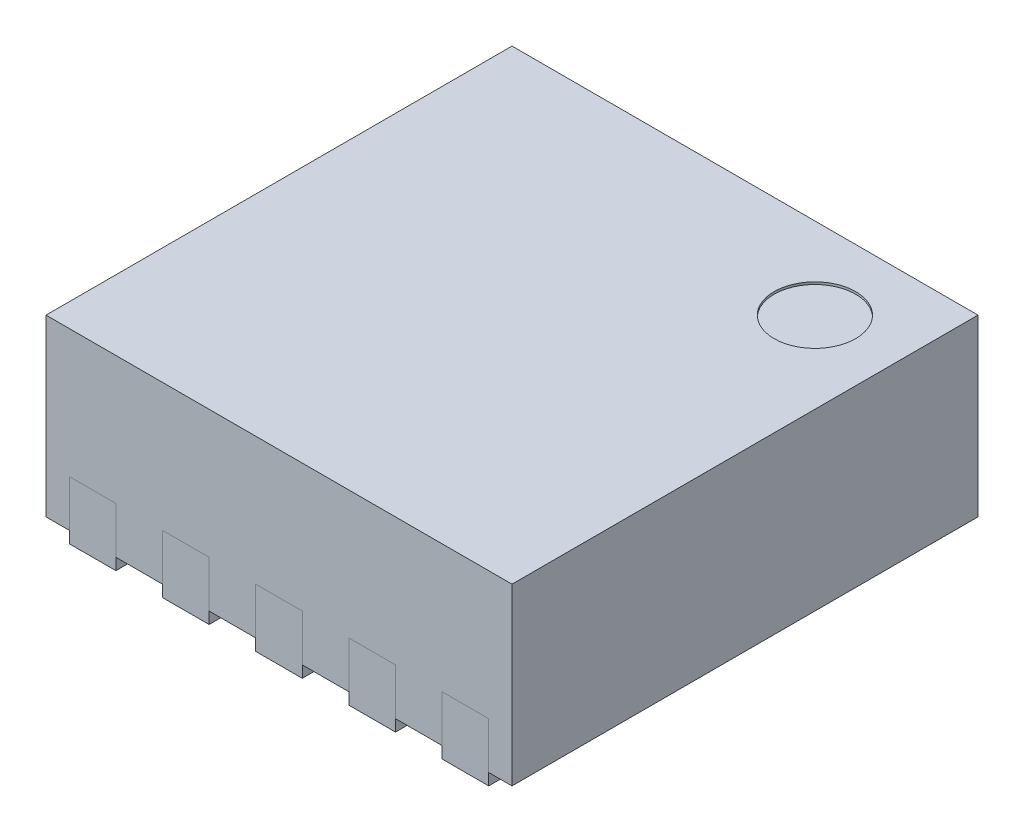
SolidWorks part; units mm, degrees
ref_plane "Front Plane" through (0, 0, 0) normal (0, 0, 1) x (1, 0, 0)
ref_plane "Top Plane" through (0, 0, 0) normal (0, 1, 0) x (1, 0, 0)
ref_plane "Right Plane" through (0, 0, 0) normal (1, 0, 0) x (0, 0, -1)
sketch "Sketch1" plane through (0, 0, 0) normal (0, 1, 0) x (1, 0, 0)
  line L1 (1, 1) -> (-1, 1)
  line L2 (1, 1) -> (1, -1)
  line L3 (1, -1) -> (-1, -1)
  line L4 (-1, 1) -> (-1, -1)
  line L5 (1, 1) -> (-1, -1) construction
  line L6 (1, -1) -> (-1, 1) construction
  point P0 (0, 0)
  dimension "D1" = 2
extrude "Boss-Extrude1" add sketch "Sketch1" along normal blind 0.75
sketch "Sketch2" plane through (0, 0, 0) normal (0, -1, 0) x (1, 0, 0)
  line L0 (0, 1) -> (0, 0) construction
  line L1 (-1, 1) -> (1, 1) construction
  line L2 (0.3, 0.7) -> (0.5, 0.7)
  line L3 (-0.1, 0.7) -> (0.1, 0.7)
  line L4 (-0.1, 0.7) -> (-0.1, 1)
  line L5 (-0.1, 1) -> (0.1, 1)
  line L6 (0.1, 0.7) -> (0.1, 1)
  line L7 (-0.1, 0.7) -> (0.1, 1) construction
  line L8 (-0.1, 1) -> (0.1, 0.7) construction
  line L9 (0.3, 0.7) -> (0.3, 1)
  line L10 (0.3, 1) -> (0.5, 1)
  line L11 (0.5, 0.7) -> (0.5, 1)
  line L12 (0.7, 0.7) -> (0.9, 0.7)
  line L13 (0.7, 0.7) -> (0.7, 1)
  line L14 (0.7, 1) -> (0.9, 1)
  line L15 (0.9, 0.7) -> (0.9, 1)
  line L16 (-0.1, 0.7) -> (0.1, 0.7)
  line L17 (-0.1, 0.7) -> (-0.1, 1)
  line L18 (-0.1, 1) -> (0.1, 1)
  line L19 (0.1, 0.7) -> (0.1, 1)
  line L20 (0.3, 0.7) -> (0.5, 0.7)
  line L21 (0.3, 0.7) -> (0.3, 1)
  line L22 (0.3, 1) -> (0.5, 1)
  line L23 (0.5, 0.7) -> (0.5, 1)
  line L24 (-0.5, 0.7) -> (-0.3, 0.7)
  line L25 (-0.5, 0.7) -> (-0.5, 1)
  line L26 (-0.5, 1) -> (-0.3, 1)
  line L27 (-0.3, 0.7) -> (-0.3, 1)
  line L28 (-0.1, 0.7) -> (0.1, 0.7)
  line L29 (-0.1, 0.7) -> (-0.1, 1)
  line L30 (-0.1, 1) -> (0.1, 1)
  line L31 (0.1, 0.7) -> (0.1, 1)
  line L32 (-0.5, 0.7) -> (-0.3, 0.7)
  line L33 (-0.5, 0.7) -> (-0.5, 1)
  line L34 (-0.5, 1) -> (-0.3, 1)
  line L35 (-0.3, 0.7) -> (-0.3, 1)
  line L36 (-0.9, 0.7) -> (-0.7, 0.7)
  line L37 (-0.9, 0.7) -> (-0.9, 1)
  line L38 (-0.9, 1) -> (-0.7, 1)
  line L39 (-0.7, 0.7) -> (-0.7, 1)
  line L40 (0, 0) -> (1, 0) construction
  line L41 (1, 1) -> (1, -1) construction
  line L42 (-0.1, -1) -> (0.1, -0.7) construction
  line L43 (-0.1, -0.7) -> (0.1, -1) construction
  line L44 (-0.7, -0.7) -> (-0.7, -1)
  line L45 (-0.9, -1) -> (-0.7, -1)
  line L46 (-0.9, -0.7) -> (-0.9, -1)
  line L47 (-0.9, -0.7) -> (-0.7, -0.7)
  line L48 (-0.3, -0.7) -> (-0.3, -1)
  line L49 (-0.5, -1) -> (-0.3, -1)
  line L50 (-0.5, -0.7) -> (-0.5, -1)
  line L51 (-0.5, -0.7) -> (-0.3, -0.7)
  line L52 (0.1, -0.7) -> (0.1, -1)
  line L53 (-0.1, -1) -> (0.1, -1)
  line L54 (-0.1, -0.7) -> (-0.1, -1)
  line L55 (-0.1, -0.7) -> (0.1, -0.7)
  line L56 (-0.3, -0.7) -> (-0.3, -1)
  line L57 (-0.5, -1) -> (-0.3, -1)
  line L58 (-0.5, -0.7) -> (-0.5, -1)
  line L59 (-0.5, -0.7) -> (-0.3, -0.7)
  line L60 (0.5, -0.7) -> (0.5, -1)
  line L61 (0.3, -1) -> (0.5, -1)
  line L62 (0.3, -0.7) -> (0.3, -1)
  line L63 (0.3, -0.7) -> (0.5, -0.7)
  line L64 (0.1, -0.7) -> (0.1, -1)
  line L65 (-0.1, -1) -> (0.1, -1)
  line L66 (-0.1, -0.7) -> (-0.1, -1)
  line L67 (-0.1, -0.7) -> (0.1, -0.7)
  line L68 (0.9, -0.7) -> (0.9, -1)
  line L69 (0.7, -1) -> (0.9, -1)
  line L70 (0.7, -0.7) -> (0.7, -1)
  line L71 (0.7, -0.7) -> (0.9, -0.7)
  line L72 (0.5, -0.7) -> (0.5, -1)
  line L73 (0.3, -1) -> (0.5, -1)
  line L74 (0.3, -0.7) -> (0.3, -1)
  line L75 (0.1, -0.7) -> (0.1, -1)
  line L76 (-0.1, -1) -> (0.1, -1)
  line L77 (-0.1, -0.7) -> (-0.1, -1)
  line L78 (-0.1, -0.7) -> (0.1, -0.7)
  line L79 (0.3, -0.7) -> (0.5, -0.7)
  line L80 (0.75, -0.25) -> (0.55, -0.45)
  line L81 (0.75, 0.45) -> (-0.75, 0.45)
  line L82 (0.75, 0.45) -> (0.75, -0.25)
  line L83 (0.55, -0.45) -> (-0.75, -0.45)
  line L84 (-0.75, 0.45) -> (-0.75, -0.45)
  line L85 (0.75, 0.45) -> (-0.75, -0.45) construction
  line L86 (0.75, -0.45) -> (-0.75, 0.45) construction
  point P5 (0, 0.85)
  point P65 (0, -0.85)
  line M10 (-1, -1) -> (1, -1)
  line M12 (1, 1) -> (-1, 1)
  dimension "D1" = 0.2
  dimension "D2" = 0.3
  dimension "D5" = 1.5
  dimension "D6" = 0.9
  dimension "D3" = 3
  dimension "D4" = 3
extrude "Cut-Extrude1" cut sketch "Sketch2" against normal blind 0.2 contours L81 L84 L83 L80 L82 | L36 L39 L37 M12 | L24 L27 L25 M12 | L3 L6 L4 M12 | L2 L11 L9 M12 | L12 L15 L13 M12 | L71 L70 L68 M10 | L63 L62 L60 M10 | L55 L54 L52 M10 | L51 L50 L48 M10 | L47 L46 L44 M10
sketch "Sketch3" plane through (0, 0.2, 0) normal (0, -1, 0) x (1, 0, 0)
  line L0 (-0.7, -0.7) -> (-0.9, -0.7) construction
  line L1 (-0.9, -0.7) -> (-0.9, -1) construction
  line L2 (-0.9, -1) -> (-0.7, -1) construction
  line L3 (-0.7, -1) -> (-0.7, -0.7) construction
  line L4 (-0.3, -0.7) -> (-0.5, -0.7) construction
  line L5 (-0.5, -0.7) -> (-0.5, -1) construction
  line L6 (-0.5, -1) -> (-0.3, -1) construction
  line L7 (-0.3, -1) -> (-0.3, -0.7) construction
  line L8 (0.1, -0.7) -> (-0.1, -0.7) construction
  line L9 (-0.1, -0.7) -> (-0.1, -1) construction
  line L10 (-0.1, -1) -> (0.1, -1) construction
  line L11 (0.1, -1) -> (0.1, -0.7) construction
  line L12 (0.9, -0.7) -> (0.7, -0.7) construction
  line L13 (0.7, -0.7) -> (0.7, -1) construction
  line L14 (0.7, -1) -> (0.9, -1) construction
  line L15 (0.9, -1) -> (0.9, -0.7) construction
  line L16 (0.5, -0.7) -> (0.3, -0.7) construction
  line L17 (0.3, -0.7) -> (0.3, -1) construction
  line L18 (0.3, -1) -> (0.5, -1) construction
  line L19 (0.5, -1) -> (0.5, -0.7) construction
  line L20 (0.75, 0.45) -> (-0.75, 0.45) construction
  line L21 (-0.75, 0.45) -> (-0.75, -0.45) construction
  line L22 (-0.75, -0.45) -> (0.55, -0.45) construction
  line L23 (0.55, -0.45) -> (0.75, -0.25) construction
  line L24 (0.75, -0.25) -> (0.75, 0.45) construction
  line L25 (0.7, 0.7) -> (0.9, 0.7) construction
  line L26 (0.9, 0.7) -> (0.9, 1) construction
  line L27 (0.9, 1) -> (0.7, 1) construction
  line L28 (0.7, 1) -> (0.7, 0.7) construction
  line L29 (0.3, 0.7) -> (0.5, 0.7) construction
  line L30 (0.5, 0.7) -> (0.5, 1) construction
  line L31 (0.5, 1) -> (0.3, 1) construction
  line L32 (0.3, 1) -> (0.3, 0.7) construction
  line L33 (-0.1, 0.7) -> (0.1, 0.7) construction
  line L34 (0.1, 0.7) -> (0.1, 1) construction
  line L35 (0.1, 1) -> (-0.1, 1) construction
  line L36 (-0.1, 1) -> (-0.1, 0.7) construction
  line L37 (-0.5, 0.7) -> (-0.3, 0.7) construction
  line L38 (-0.3, 0.7) -> (-0.3, 1) construction
  line L39 (-0.3, 1) -> (-0.5, 1) construction
  line L40 (-0.5, 1) -> (-0.5, 0.7) construction
  line L41 (-0.9, 0.7) -> (-0.7, 0.7) construction
  line L42 (-0.7, 0.7) -> (-0.7, 1) construction
  line L43 (-0.7, 1) -> (-0.9, 1) construction
  line L44 (-0.9, 1) -> (-0.9, 0.7) construction
  line L45 (-0.7, -0.7) -> (-0.9, -0.7)
  line L46 (-0.9, -0.7) -> (-0.9, -1)
  line L47 (-0.9, -1) -> (-0.7, -1)
  line L48 (-0.7, -1) -> (-0.7, -0.7)
  line L49 (-0.3, -0.7) -> (-0.5, -0.7)
  line L50 (-0.5, -0.7) -> (-0.5, -1)
  line L51 (-0.5, -1) -> (-0.3, -1)
  line L52 (-0.3, -1) -> (-0.3, -0.7)
  line L53 (0.1, -0.7) -> (-0.1, -0.7)
  line L54 (-0.1, -0.7) -> (-0.1, -1)
  line L55 (-0.1, -1) -> (0.1, -1)
  line L56 (0.1, -1) -> (0.1, -0.7)
  line L57 (0.9, -0.7) -> (0.7, -0.7)
  line L58 (0.7, -0.7) -> (0.7, -1)
  line L59 (0.7, -1) -> (0.9, -1)
  line L60 (0.9, -1) -> (0.9, -0.7)
  line L61 (0.5, -0.7) -> (0.3, -0.7)
  line L62 (0.3, -0.7) -> (0.3, -1)
  line L63 (0.3, -1) -> (0.5, -1)
  line L64 (0.5, -1) -> (0.5, -0.7)
  line L65 (0.75, 0.45) -> (-0.75, 0.45)
  line L66 (-0.75, 0.45) -> (-0.75, -0.45)
  line L67 (-0.75, -0.45) -> (0.55, -0.45)
  line L68 (0.55, -0.45) -> (0.75, -0.25)
  line L69 (0.75, -0.25) -> (0.75, 0.45)
  line L70 (0.7, 0.7) -> (0.9, 0.7)
  line L71 (0.9, 0.7) -> (0.9, 1)
  line L72 (0.9, 1) -> (0.7, 1)
  line L73 (0.7, 1) -> (0.7, 0.7)
  line L74 (0.3, 0.7) -> (0.5, 0.7)
  line L75 (0.5, 0.7) -> (0.5, 1)
  line L76 (0.5, 1) -> (0.3, 1)
  line L77 (0.3, 1) -> (0.3, 0.7)
  line L78 (-0.1, 0.7) -> (0.1, 0.7)
  line L79 (0.1, 0.7) -> (0.1, 1)
  line L80 (0.1, 1) -> (-0.1, 1)
  line L81 (-0.1, 1) -> (-0.1, 0.7)
  line L82 (-0.5, 0.7) -> (-0.3, 0.7)
  line L83 (-0.3, 0.7) -> (-0.3, 1)
  line L84 (-0.3, 1) -> (-0.5, 1)
  line L85 (-0.5, 1) -> (-0.5, 0.7)
  line L86 (-0.9, 0.7) -> (-0.7, 0.7)
  line L87 (-0.7, 0.7) -> (-0.7, 1)
  line L88 (-0.7, 1) -> (-0.9, 1)
  line L89 (-0.9, 1) -> (-0.9, 0.7)
extrude "Boss-Extrude2" add sketch "Sketch3" along normal blind 0.25 separate body
sketch "Sketch4" plane through (0, 0.75, 0) normal (0, 1, 0) x (1, 0, 0)
  line L1 (1, 1) -> (0.65, 1) construction
  line L2 (1, 1) -> (1, 0.65) construction
  line L3 (1, 0.65) -> (0.65, 0.65) construction
  line L4 (0.65, 1) -> (0.65, 0.65) construction
  circle A0 centre (0.65, 0.65) radius 0.175
  point P6 (0, 0)
  dimension "D1" = 0.35
  dimension "D2" = 0.35
extrude "Cut-Extrude2" cut sketch "Sketch4" against normal blind 0.01
